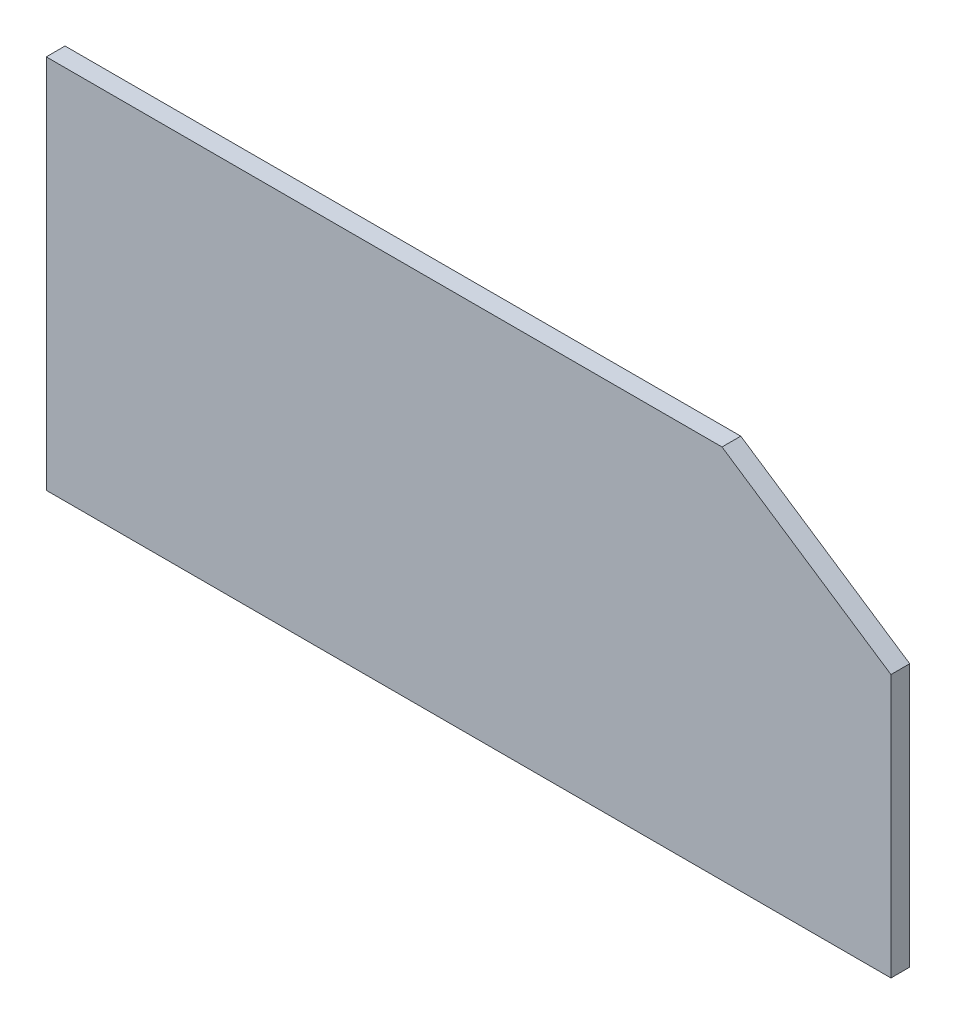
SolidWorks part; units mm, degrees
ref_plane "Front Plane" through (0, 0, 0) normal (0, 0, 1) x (1, 0, 0)
ref_plane "Top Plane" through (0, 0, 0) normal (0, 1, 0) x (1, 0, 0)
ref_plane "Right Plane" through (0, 0, 0) normal (1, 0, 0) x (0, 0, -1)
sketch "Sketch1" plane through (0, 0, 0) normal (0, 0, 1) x (1, 0, 0)
  line L0 (-150.0119, -117.3034) -> (-7.1369, -117.3034)
  line L1 (-7.1369, -117.3034) -> (-7.1369, -72.8534)
  line L2 (-7.1369, -72.8534) -> (-35.7119, -53.8034)
  line L3 (-35.7119, -53.8034) -> (-150.0119, -53.8034)
  line L4 (-150.0119, -53.8034) -> (-150.0119, -117.3034)
extrude "Boss-Extrude1" add sketch "Sketch1" along normal mid plane 3.175
